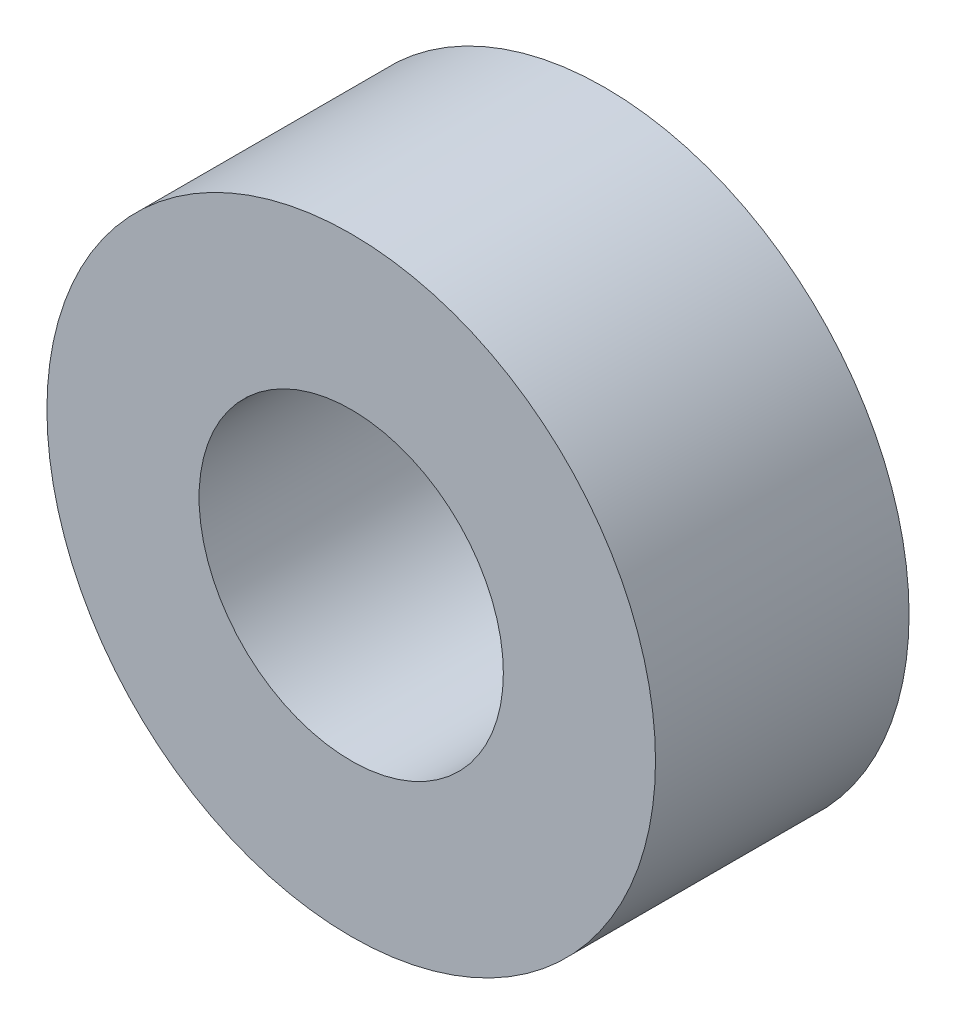
SolidWorks part; units mm, degrees
ref_plane "Front Plane" through (0, 0, 0) normal (0, 0, 1) x (1, 0, 0)
ref_plane "Top Plane" through (0, 0, 0) normal (0, 1, 0) x (1, 0, 0)
ref_plane "Right Plane" through (0, 0, 0) normal (1, 0, 0) x (0, 0, -1)
sketch "Sketch1" plane through (0, 0, 0) normal (0, 0, 1) x (1, 0, 0)
  circle A0 centre (0, 0) radius 3
  circle A1 centre (0, 0) radius 1.5
extrude "Extrude1" add sketch "Sketch1" along normal blind 2.5
